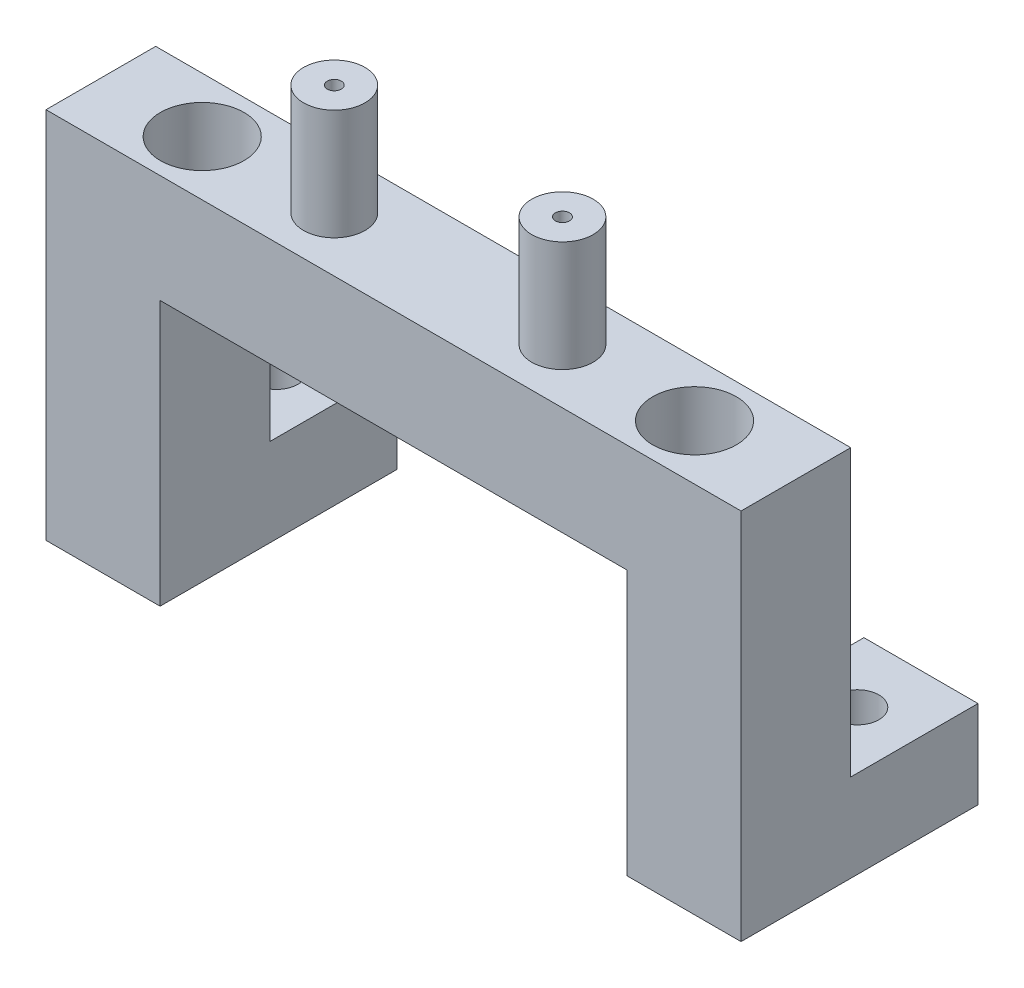
SolidWorks part; units mm, degrees
ref_plane "Front Plane" through (0, 0, 0) normal (0, 0, 1) x (1, 0, 0)
ref_plane "Top Plane" through (0, 0, 0) normal (0, 1, 0) x (1, 0, 0)
ref_plane "Right Plane" through (0, 0, 0) normal (1, 0, 0) x (0, 0, -1)
sketch "Sketch6" plane through (0, 0, 0) normal (0, 0, 1) x (1, 0, 0)
  line L0 (-54.6933, -23.3702) -> (-54.6933, 19.1298)
  line L1 (-54.6933, 19.1298) -> (-15.0933, 19.1298)
  line L2 (-54.6933, -23.3702) -> (-41.6933, -23.3702)
  line L3 (-41.6933, -23.3702) -> (-41.6933, 6.8039)
  line L4 (-41.6933, 6.8039) -> (-15.0933, 6.8039)
  line L5 (-15.0933, 6.8039) -> (-15.0933, 19.1298)
  dimension "D1" = 39.6
  dimension "D2" = 13
  dimension "D3" = 42.5
extrude "Boss-Extrude1" add sketch "Sketch6" along normal blind 12.5 contours L5 L1 L0 L2 L3 L4
sketch "Sketch8" plane through (0, 0, 0) normal (0, 0, -1) x (-1, 0, 0)
  line L0 (41.6933, -23.3702) -> (41.6933, 6.8039) construction
  line L1 (54.6933, -23.3702) -> (41.6933, -23.3702)
  line L2 (54.6933, -23.3702) -> (54.6933, -13.3702)
  line L3 (54.6933, -13.3702) -> (41.6933, -13.3702)
  line L4 (41.6933, -23.3702) -> (41.6933, -13.3702)
  dimension "D1" = 10
extrude "Boss-Extrude2" add sketch "Sketch8" along normal blind 14.5 contours L2 L1 L4 L3
mirror "Mirror1" about plane through (-15.0933, 6.8039, 12.5) normal (-1, 0, 0) of bodies 110
sketch "Sketch9" plane through (0, -13.3702, 0) normal (0, 1, 0) x (1, 0, 0)
  line L0 (-48.1933, 14.5) -> (-48.1933, 0) construction
  line L1 (-54.6933, 14.5) -> (-41.6933, 14.5) construction
  line L2 (-54.6933, 0) -> (-41.6933, 0) construction
  line L3 (18.0067, 14.5) -> (18.0067, 0) construction
  line L4 (24.5067, 14.5) -> (11.5067, 14.5) construction
  line L5 (24.5067, 0) -> (11.5067, 0) construction
  point P4 (-54.6933, 14.5)
hole_wizard "#10 (0.1935) Diameter Hole1" positions "Sketch10" profile "Sketch12" hole size "#10" standard "ANSI Inch" end condition through all
sketch "Sketch10" plane through (0, -13.3702, 0) normal (0, 1, 0) x (1, 0, 0)
  line L0 (-48.1933, 14.5) -> (-48.1933, 0) construction
  line L1 (18.0067, 14.5) -> (18.0067, 0) construction
  point P0 (-48.1933, 7.25)
  point P4 (18.0067, 7.25)
sketch "Sketch12" plane through (-48.1933, -13.3702, -7.25) normal (1, 0, 0) x (0, 0, 1)
  line L0 (0, 0) -> (0, 10)
  line L1 (0, 10) -> (2.4574, 10)
  line L2 (2.4574, 10) -> (2.4574, 0)
  line L5 (2.4574, 0) -> (0, 0)
  line L11 (0, -6.35) -> (0, 107.95) construction
  dimension "Thru Hole Dia." = 4.9149
  dimension "Thru Hole Depth" = 10
sketch "Sketch14" plane through (0, 19.1298, 0) normal (0, 1, 0) x (1, 0, 0)
  line L0 (-54.6933, -6.25) -> (24.5067, -6.25) construction
  line L1 (-54.6933, -12.5) -> (-54.6933, 0) construction
  line L2 (24.5067, -12.5) -> (24.5067, 0) construction
  line L3 (-15.0933, -6.25) -> (-2.0933, -6.25)
  line L4 (-15.0933, -6.25) -> (-28.0933, -6.25)
  circle A0 centre (-28.0933, -6.25) radius 3.5
  circle A1 centre (-2.0933, -6.25) radius 3.5
  dimension "D1" = 13
  dimension "D2" = 13
extrude "Boss-Extrude3" add sketch "Sketch14" along normal blind 12.6 contours L3 L0 A1 | A0
ref_plane "Plane23" through (24.5067, 19.1298, 0) normal (0, 0, -1) x (-1, 0, 0)
sketch "Sketch18" plane through (0, 19.1298, 0) normal (0, 1, 0) x (1, 0, 0)
  line L0 (24.5067, -6.25) -> (1.4067, -6.25) construction
  line L1 (24.5067, -12.5) -> (24.5067, 0) construction
  circle A0 centre (-2.0933, -6.25) radius 3.5 construction
  point P7 (12.9567, -6.25)
  point P8 (0, 0)
sketch "Sketch23" plane through (0, 31.7298, 0) normal (0, 1, 0) x (1, 0, 0)
  circle A0 centre (-2.0933, -6.25) radius 0.8
extrude "Cut-Extrude3" cut sketch "Sketch23" against normal blind 30
sketch "Sketch24" plane through (0, 31.7298, 0) normal (0, 1, 0) x (1, 0, 0)
  circle A0 centre (-28.0933, -6.25) radius 0.8
extrude "Cut-Extrude4" cut sketch "Sketch24" against normal blind 30 contours A0
ref_plane "Plane28" through (-54.6933, 19.1298, 0) normal (0, 0, -1) x (-1, 0, 0)
sketch "Sketch30" plane through (0, 19.1298, 0) normal (0, 1, 0) x (1, 0, 0)
  line L0 (-31.5933, -6.25) -> (-54.6933, -6.25) construction
  line L2 (-54.6933, -12.5) -> (-54.6933, 0) construction
  circle A1 centre (-28.0933, -6.25) radius 3.5 construction
  point P2 (-54.6933, -6.25)
  point P5 (-31.5933, -6.25)
  point P7 (-43.1433, -6.25)
  point P8 (-7.0293, -0.8851)
hole_wizard "3/8 (0.375) Diameter Hole5" positions "3DSketch5" profile "Sketch33" hole size "3/8" standard "ANSI Inch"
sketch3d "3DSketch5"
  point P0 (-43.1433, 19.1298, 6.25)
  point P3 (12.9567, 19.1298, 6.25)
sketch "Sketch33" plane through (-43.1433, 19.1298, 6.25) normal (1, 0, 0) x (0, 0, 1)
  line L0 (0, 0) -> (0, 12.8616)
  line L1 (0, 12.8616) -> (4.7625, 10)
  line L2 (4.7625, 10) -> (4.7625, 0)
  line L5 (4.7625, 0) -> (0, 0)
  line L10 (0, 12.8616) -> (-4.7625, 10) construction
  line L11 (0, -6.35) -> (0, 107.95) construction
  dimension "Hole Dia." = 9.525
  dimension "Hole Depth" = 10
  dimension "Drill Angle" = 118
